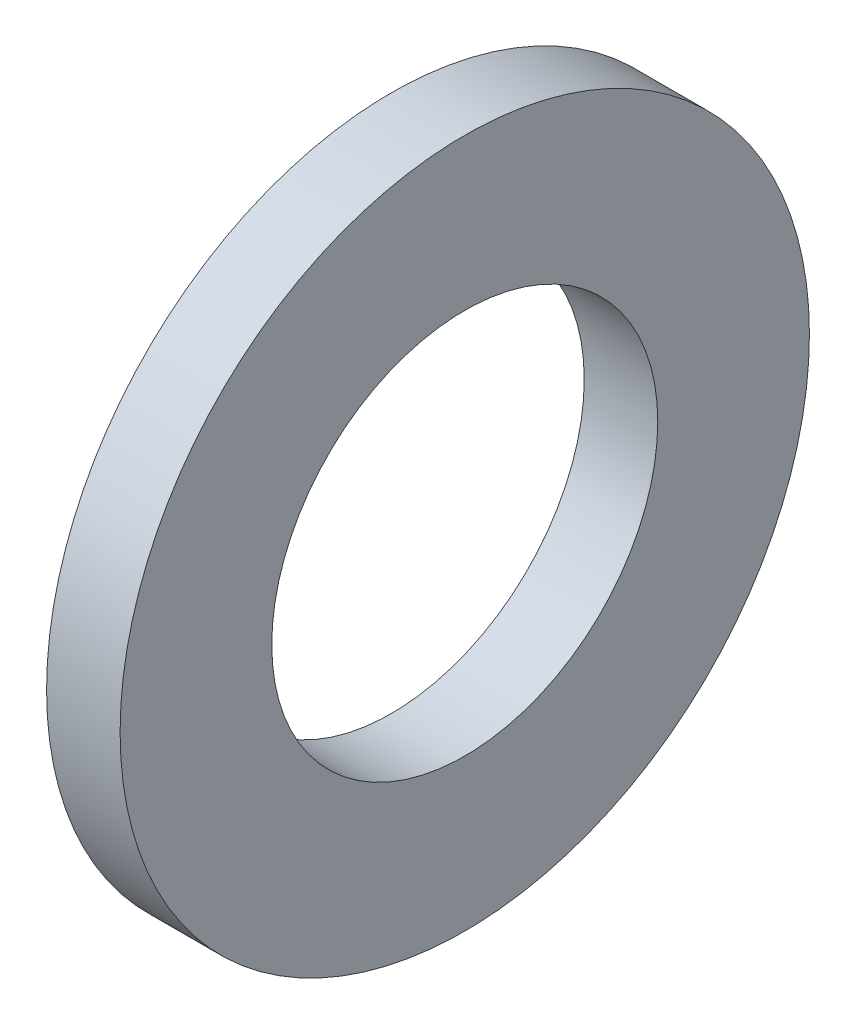
SolidWorks part; units mm, degrees
ref_plane "Plane1" through (0, 0, 0) normal (0, 0, 1) x (1, 0, 0)
ref_plane "Plane2" through (0, 0, 0) normal (0, 1, 0) x (1, 0, 0)
ref_plane "Plane3" through (0, 0, 0) normal (1, 0, 0) x (0, 0, -1)
revolve "Base-Revolve" add sketch "Sketch1" angle 360 about L0
sketch "Sketch1" plane through (0, 0, 0) normal (0, 0, 1) x (1, 0, 0)
  line L0 (-34.925, 0) -> (9.525, 0) construction
  line L1 (0, 4.2) -> (0, 7.5)
  line L2 (0, 7.5) -> (-1.6, 7.5)
  line L3 (-1.6, 7.5) -> (-1.6, 4.2)
  line L4 (-1.6, 4.2) -> (0, 4.2)
  dimension "Thickness" = 1.6
  dimension "Inside_dia" = 8.4
  dimension "Outside_dia" = 15
